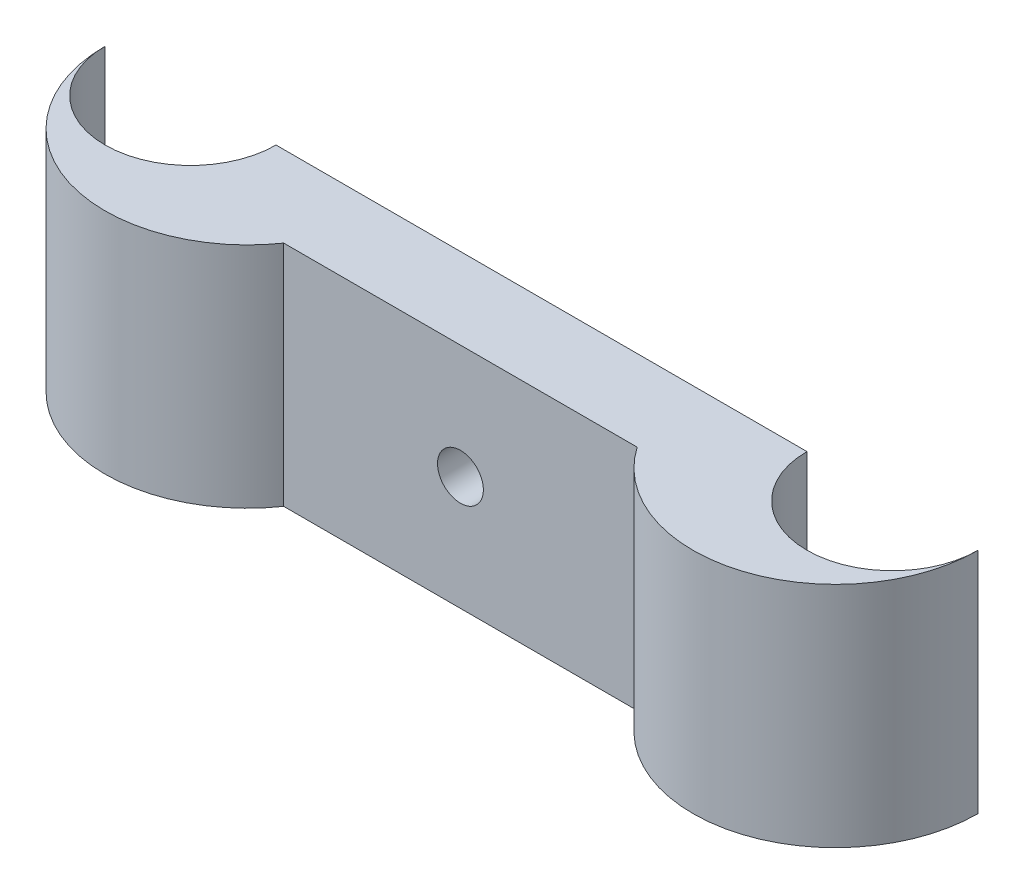
SolidWorks part; units mm, degrees
ref_plane "Front Plane" through (0, 0, 0) normal (0, 0, 1) x (1, 0, 0)
ref_plane "Top Plane" through (0, 0, 0) normal (0, 1, 0) x (1, 0, 0)
ref_plane "Right Plane" through (0, 0, 0) normal (1, 0, 0) x (0, 0, -1)
sketch "Sketch1" plane through (0, 0, 0) normal (0, 1, 0) x (1, 0, 0)
  line L0 (-30.78, 0) -> (30.78, 0) construction
  line L1 (-23.28, 0) -> (23.28, 0)
  line L2 (-15.4991, -7.11) -> (15.4991, -7.11)
  arc A0 (-38.28, 0) -> (-23.28, 0) centre (-30.78, 0) ccw
  arc A1 (23.28, 0) -> (38.28, 0) centre (30.78, 0) ccw
  arc A3 (-38.28, 0) -> (-15.4991, -7.11) centre (-25.78, 0) ccw
  arc A4 (15.4991, -7.11) -> (38.28, 0) centre (25.78, 0) ccw
  point P4 (0, 0)
  dimension "D2" = 15
  dimension "D3" = 15
  dimension "D4" = 25
  dimension "D5" = 25
  dimension "D1" = 61.56
  dimension "D6" = 7.11
extrude "Boss-Extrude1" add sketch "Sketch1" along normal blind 20
sketch "Sketch2" plane through (0, 0, 0) normal (0, 0, -1) x (-1, 0, 0)
  line L0 (-23.28, 10) -> (23.28, 10) construction
  line L1 (-23.28, 20) -> (-23.28, 0) construction
  line L2 (23.28, 20) -> (23.28, 0) construction
  circle A0 centre (0, 10) radius 2.01
  dimension "D1" = 4.02
extrude "Cut-Extrude1" cut sketch "Sketch2" against normal blind 20
